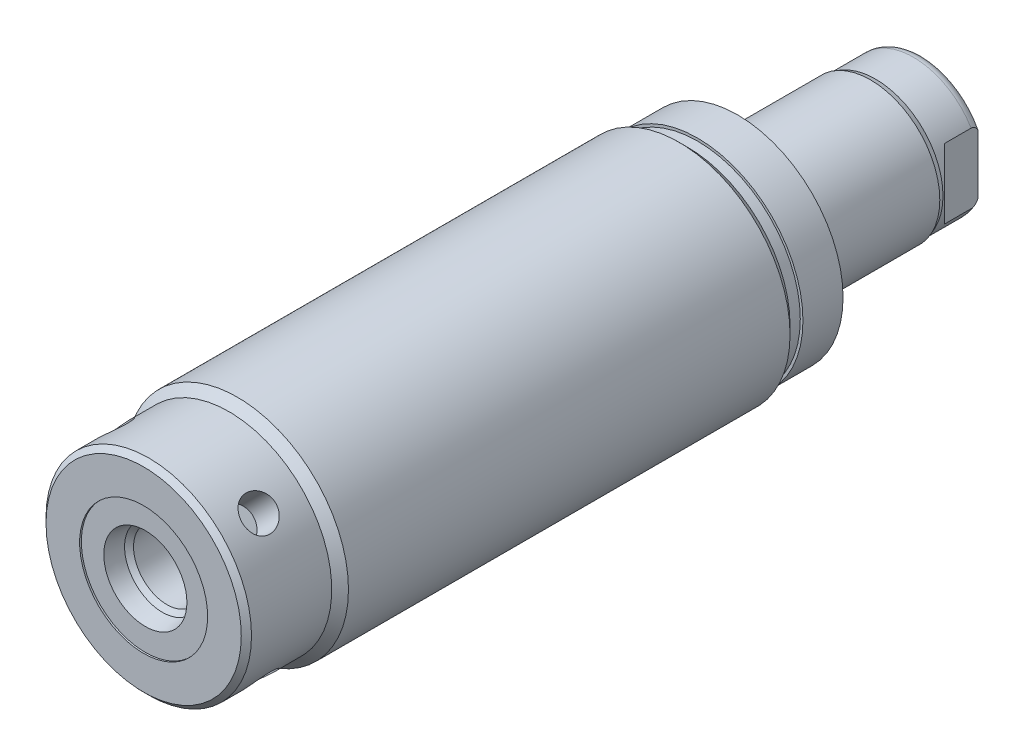
SolidWorks part; units mm, degrees
material "Alloy Steel"
ref_plane "Front Plane" through (0, 0, 0) normal (0, 0, 1) x (1, 0, 0)
ref_plane "Top Plane" through (0, 0, 0) normal (0, 1, 0) x (1, 0, 0)
ref_plane "Right Plane" through (0, 0, 0) normal (1, 0, 0) x (0, 0, -1)
ref_plane "Plane1" through (0, 0, 0) normal (0, 0, 1) x (1, 0, 0)
sketch "Sketch1" plane through (0, 0, 0) normal (0, 0, 1) x (1, 0, 0)
  circle A0 centre (0, 0) radius 16.5354
  dimension "D1" = 33.0708
extrude "Extrude1" add sketch "Sketch1" along normal blind 82.423
sketch "Sketch2" plane through (0, 0, 0) normal (0, 1, 0) x (1, 0, 0)
  line L0 (16.5354, -82.423) -> (16.5354, -68.4784)
  line L1 (16.5354, -68.4784) -> (15.2908, -69.723)
  line L2 (15.2908, -69.723) -> (15.2908, -82.423)
  line L3 (15.2908, -82.423) -> (16.5354, -82.423)
  line L4 (0, 0) -> (0, -24.4965) construction
  line L5 (-16.5354, -82.423) -> (16.5354, -82.423) construction
  line L6 (16.5354, -82.423) -> (16.5354, 0) construction
  dimension "D1" = 12.7
  dimension "D2" = 30.5816
  dimension "D3" = 45
revolve "Cut-Revolve1" cut sketch "Sketch2" angle 360 about L4
sketch "Sketch3" plane through (0, 0, 0) normal (0, 1, 0) x (1, 0, 0)
  line L0 (15.2908, 0) -> (15.2908, -1.524)
  line L1 (15.2908, -1.524) -> (16.5354, -2.7686)
  line L2 (16.5354, -2.7686) -> (16.5354, 0)
  line L3 (16.5354, 0) -> (15.2908, 0)
  line L4 (0, 0) -> (0, 3.0455) construction
  line L5 (15.2908, -82.423) -> (15.2908, -69.723) construction
  line L6 (16.5354, 0) -> (-16.5354, 0) construction
  line L7 (16.5354, -68.4784) -> (16.5354, 0) construction
  dimension "D1" = 45
  dimension "D2" = 1.524
revolve "Cut-Revolve2" cut sketch "Sketch3" angle 360 about L4
sketch "S2D0002" plane through (0, 0, 0) normal (0, 1, 0) x (1, 0, 0)
  line L0 (6.1849, -82.169) -> (9.525, -82.169)
  line L1 (6.1849, -82.169) -> (5.6423, -79.6163)
  line L2 (5.6423, -79.6163) -> (4.9784, -78.9524)
  line L3 (4.9784, -78.9524) -> (4.9784, -68.199)
  line L4 (4.9784, -68.199) -> (0, -68.199)
  line L5 (0, -68.199) -> (0, -82.423)
  line L6 (0, -14.6685) -> (0, 0.6985) construction
  line L8 (9.525, -82.169) -> (9.525, -82.423)
  line L9 (-15.2908, -82.423) -> (15.2908, -82.423) construction
  line L10 (9.525, -82.423) -> (0, -82.423)
  dimension "D1" = 19.05
  dimension "D2" = 9.9568
  dimension "D3" = 0.254
  dimension "D4" = 12.3698
  dimension "D5" = 12
  dimension "D6" = 45
  dimension "D7" = 2.5527
  dimension "D8" = 13.97
revolve "Cut-Revolve3" cut sketch "S2D0002" angle 360 about L6
chamfer "Chamfer1" distance 0.762 angle 45 1 edges at (-15.2908, 0, 82.423)
sketch "Sketch6" plane through (0, 0, 0) normal (0, 0, -1) x (-1, 0, 0)
  circle A0 centre (0, 0) radius 15.6845
  circle A1 centre (0, 0) radius 16.5354 construction
  dimension "D1" = 31.369
extrude "Extrude2" add sketch "Sketch6" along normal blind 5.969
sketch "Sketch7" plane through (0, 0, 0) normal (1, 0, 0) x (0, 0, -1)
  line L0 (5.969, 0) -> (5.969, -10.3187)
  line L1 (5.969, -10.3187) -> (33.147, -10.3187)
  line L2 (33.147, -10.3187) -> (33.147, 0)
  line L3 (33.147, 0) -> (5.969, 0)
  line L4 (0, 0) -> (9.7123, 0) construction
  line L5 (5.969, -15.6845) -> (5.969, 15.6845) construction
  dimension "D1" = 20.6375
  dimension "D2" = 27.178
revolve "Revolve1" add sketch "Sketch7" angle 360 about L4
sketch "S2D0001" plane through (0, 0, 0) normal (0, 1, 0) x (1, 0, 0)
  line L0 (3.2639, 31.2113) -> (3.2639, 18.2118)
  line L1 (3.2639, 18.2118) -> (0, 18.2118)
  line L2 (4.3815, 33.147) -> (0, 33.147)
  line L3 (0, 33.147) -> (0, 18.2118)
  line L4 (3.2639, 31.2113) -> (4.3815, 33.147)
  line L5 (0, -31.3084) -> (0, 2.765) construction
  line L6 (10.3188, 33.147) -> (-10.3188, 33.147) construction
  dimension "D1" = 8.763
  dimension "D2" = 30
  dimension "D3" = 14.9352
  dimension "D4" = 6.5278
revolve "Cut-Revolve5" cut sketch "S2D0001" angle 360 about L5
ref_plane "Plane8" through (0, 0, 0) normal (1, 0, 0) x (0, -1, 0)
sketch "Sketch9" plane through (0, 0, 0) normal (1, 0, 0) x (0, -1, 0)
  line L0 (-10.3188, 25.7302) -> (-10.033, 26.4922)
  line L1 (-10.033, 26.4922) -> (-10.033, 32.131)
  line L2 (0, 12.6594) -> (0, 20.8178) construction
  line L3 (10.3187, 33.147) -> (-10.3188, 33.147) construction
  line L4 (-9.6449, 33.147) -> (-10.3188, 33.147)
  line L5 (-10.3188, 33.147) -> (-10.3188, 25.7302)
  arc A0 (-9.6449, 33.147) -> (-10.033, 32.131) centre (-8.509, 32.131) ccw
  dimension "D1" = 1.524
  dimension "D2" = 1.016
  dimension "D3" = 20.066
  dimension "D4" = 0.762
  dimension "D5" = 7.4168
revolve "Cut-Revolve6" cut sketch "Sketch9" angle 360 about L2
sketch "Sketch13" plane through (0, 0, 0) normal (0, 1, 0) x (1, 0, 0)
  line L0 (8.5852, 33.147) -> (8.5852, 28.194)
  line L1 (8.5852, 28.194) -> (10.033, 26.7462)
  line L2 (-8.5852, 33.147) -> (-8.5852, 28.194)
  line L3 (-8.5852, 28.194) -> (-10.033, 26.7462)
  line L4 (9.6449, 33.147) -> (-9.6449, 33.147) construction
  line L5 (0, 13.7262) -> (0, 20.767) construction
  line L6 (10.033, 26.7462) -> (10.033, 33.147)
  line L8 (8.5852, 33.147) -> (10.033, 33.147)
  line L9 (10.033, 26.4922) -> (10.033, 32.131) construction
  line L10 (-10.033, 26.7462) -> (-10.033, 33.147)
  line L11 (-8.5852, 33.147) -> (-10.033, 33.147)
  dimension "D1" = 17.1704
  dimension "D2" = 135
  dimension "D3" = 4.953
extrude "Cut-Extrude4" cut sketch "Sketch13" against normal mid plane 39.685
ref_plane "Plane13" through (0, 0, 0) normal (0.7071, 0.7071, 0) x (0, 0, -1)
hole_wizard "Hole1" positions "3DSketch2" profile "Sketch14" legacy
sketch3d "3DSketch2"
  point P0 (-10.8122, 10.8122, 76.073)
  dimension "D1" = 6.35
sketch "Sketch14" plane through (-10.8122, 10.8122, 76.073) normal (0, 0, 1) x (-0.7071, -0.7071, 0)
  line L0 (0, 0) -> (0, 4.7498)
  line L1 (0, 4.7498) -> (2.5019, 4.7498)
  line L2 (2.5019, 4.7498) -> (2.5019, 0)
  line L3 (2.5019, 0) -> (0, 0)
  line L4 (0, 110) -> (0, -10) construction
  dimension "Diameter" = 5.0038
  dimension "Depth" = 4.7498
pattern_circular "CirPattern1" count 4 over 360 about axis through (0, 0, 0) along (0, 0, 1) of "Hole1"
